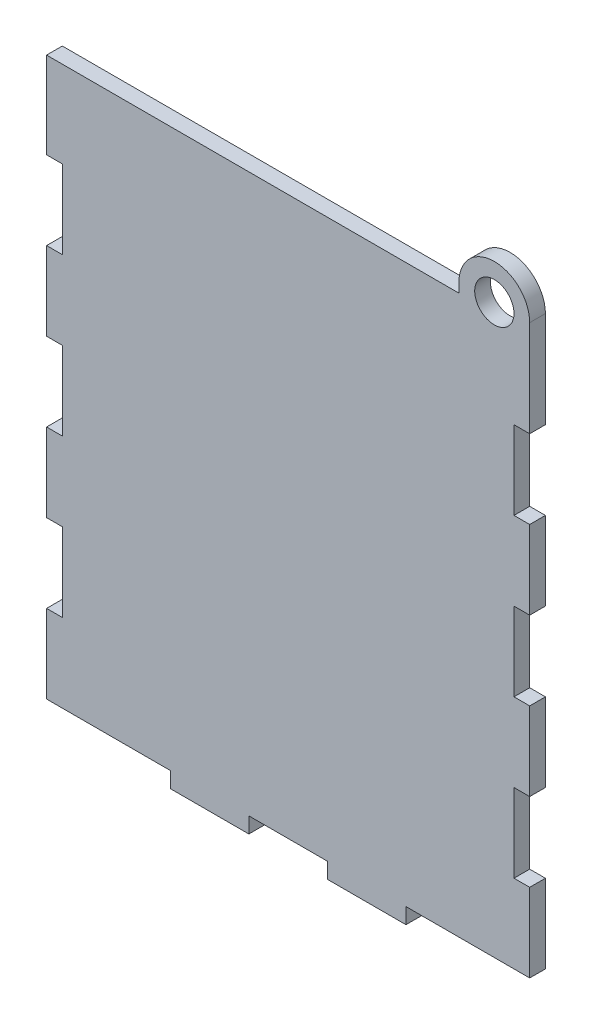
SolidWorks part; units mm, degrees
ref_plane "Спереди" through (0, 0, 0) normal (0, 0, 1) x (1, 0, 0)
ref_plane "Сверху" through (0, 0, 0) normal (0, 1, 0) x (1, 0, 0)
ref_plane "Справа" through (0, 0, 0) normal (1, 0, 0) x (0, 0, -1)
sketch "Эскиз1" plane through (0, 0, 0) normal (0, 0, 1) x (1, 0, 0)
  line L0 (31.5, 0) -> (31.5, -4)
  line L1 (0, 0) -> (31.5, 0)
  line L2 (0, 0) -> (0, 20)
  line L3 (0, 142) -> (105, 142)
  line L4 (123, 0) -> (123, 20)
  line L5 (31.5, -4) -> (51.5, -4)
  line L6 (51.5, -4) -> (51.5, 0)
  line L7 (71.5, 0) -> (71.5, -4)
  line L8 (71.5, -4) -> (91.5, -4)
  line L9 (91.5, -4) -> (91.5, 0)
  line L10 (51.5, 0) -> (71.5, 0)
  line L11 (91.5, 0) -> (123, 0)
  line L13 (105, 144.5) -> (105, 142)
  line L14 (0, 120) -> (4, 120)
  line L15 (4, 120) -> (4, 100)
  line L16 (4, 100) -> (0, 100)
  line L17 (0, 80) -> (4, 80)
  line L18 (4, 80) -> (4, 60)
  line L19 (4, 60) -> (0, 60)
  line L20 (61.5, 0) -> (61.5, 70.5274) construction
  line L21 (119, 60) -> (123, 60)
  line L22 (119, 80) -> (119, 60)
  line L23 (123, 80) -> (119, 80)
  line L24 (119, 100) -> (123, 100)
  line L25 (119, 120) -> (119, 100)
  line L26 (123, 120) -> (119, 120)
  line L27 (123, 120) -> (123, 144.5)
  line L28 (123, 80) -> (123, 100)
  line L29 (0, 80) -> (0, 100)
  line L30 (0, 120) -> (0, 142)
  line L31 (0, 40) -> (4, 40)
  line L32 (4, 40) -> (4, 20)
  line L33 (4, 20) -> (0, 20)
  line L34 (119, 20) -> (123, 20)
  line L35 (119, 40) -> (119, 20)
  line L36 (123, 40) -> (119, 40)
  line L37 (0, 40) -> (0, 60)
  line L38 (123, 40) -> (123, 60)
  circle A0 centre (114, 144.5) radius 5
  arc A1 (123, 144.5) -> (105, 144.5) centre (114, 144.5) ccw
  point P44 (123, 121.8291)
  point P45 (123, 130.3662)
  point P46 (123, 143.8333)
  dimension "D7" = 10
  dimension "D8" = 18
  dimension "D1" = 123
  dimension "D2" = 20
  dimension "D3" = 4
  dimension "D4" = 20
  dimension "D6" = 2.5
  dimension "D9" = 142
  dimension "D10" = 4
  dimension "D11" = 20
  dimension "D12" = 20
  dimension "D14" = 20
  dimension "D5" = 2
  dimension "D13" = 3
extrude "Бобышка-Вытянуть1" add sketch "Эскиз1" along normal blind 4
